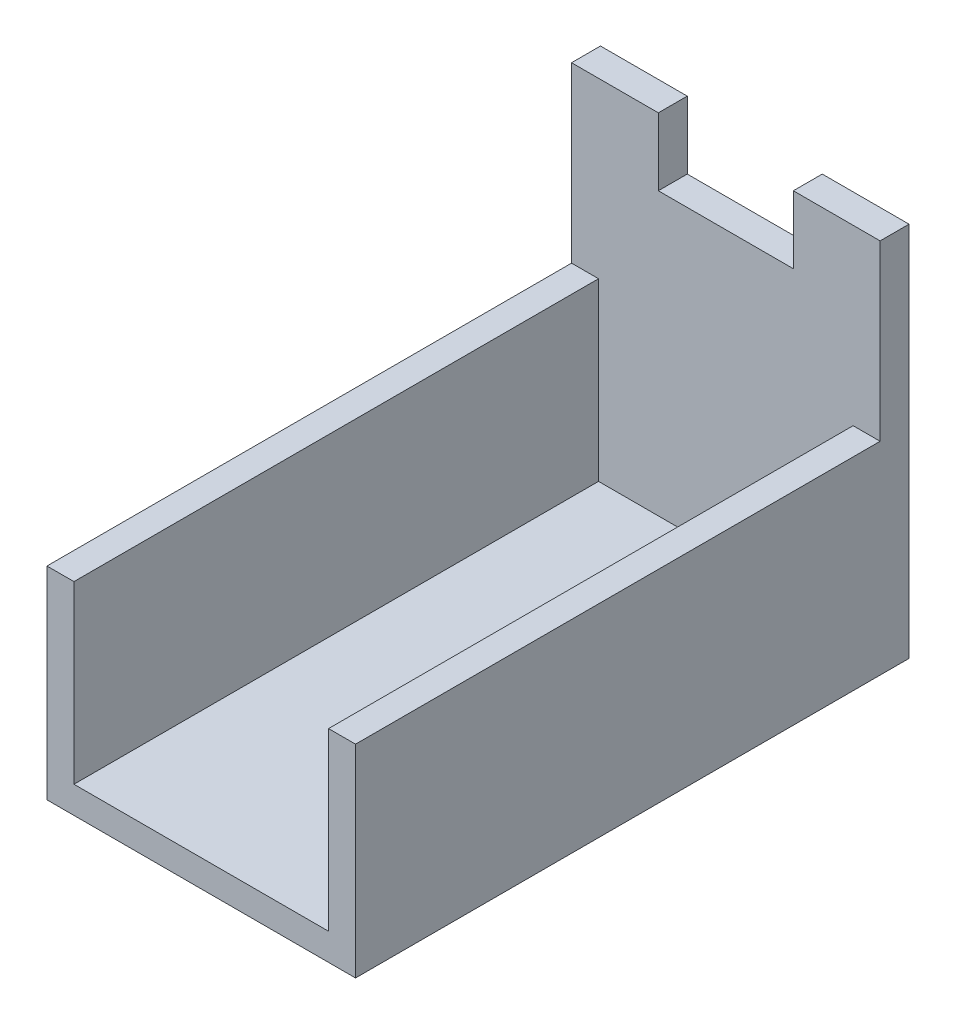
SolidWorks part; units mm, degrees
ref_plane "Front Plane" through (0, 0, 0) normal (0, 0, 1) x (1, 0, 0)
ref_plane "Top Plane" through (0, 0, 0) normal (0, 1, 0) x (1, 0, 0)
ref_plane "Right Plane" through (0, 0, 0) normal (1, 0, 0) x (0, 0, -1)
sketch "Sketch1" plane through (0, 0, 0) normal (0, 0, 1) x (1, 0, 0)
  line L0 (-1.524, 1.6923) -> (-1.524, 13.2493)
  line L1 (-1.524, 13.2493) -> (0.254, 13.2493)
  line L2 (0.254, 13.2493) -> (0.254, -0.0857)
  line L3 (0.254, -0.0857) -> (-20.066, -0.0857)
  line L4 (-20.066, -0.0857) -> (-20.066, 13.2493)
  line L5 (-20.066, 13.2493) -> (-18.288, 13.2493)
  line L6 (-18.288, 13.2493) -> (-18.288, 1.6923)
  line L7 (-18.288, 1.6923) -> (-1.524, 1.6923)
  point P2 (0, 0)
  dimension "D1" = 11.557
  dimension "D2" = 16.764
extrude "Boss-Extrude1" add sketch "Sketch1" against normal blind 36.449
sketch "Sketch3" plane through (0, 1.6923, 0) normal (0, 1, 0) x (1, 0, 0)
  line L0 (-18.288, 36.449) -> (-1.524, 36.449)
  line L1 (-1.524, 36.449) -> (-1.524, 34.544)
  line L2 (-1.524, 36.449) -> (-1.524, 0) construction
  line L3 (-1.524, 34.544) -> (-18.288, 34.544)
  line L4 (-18.288, 36.449) -> (-18.288, 0) construction
  line L5 (-18.288, 34.544) -> (-18.288, 36.449)
extrude "Boss-Extrude3" add sketch "Sketch3" along normal up to surface (11.557 mm away) up to face at (-19.177, 13.2493, -18.2245)
sketch "Sketch4" plane through (0, 13.2493, 0) normal (0, 1, 0) x (1, 0, 0)
  line L0 (-9.906, 34.544) -> (0.254, 34.544)
  line L1 (-18.288, 34.544) -> (-1.524, 34.544) construction
  line L2 (0.254, 36.449) -> (0.254, 0) construction
  line L3 (0.254, 34.544) -> (0.254, 36.449)
  line L4 (0.254, 36.449) -> (-20.066, 36.449)
  line L5 (-20.066, 36.449) -> (-20.066, 34.544)
  line L6 (-20.066, 36.449) -> (-20.066, 0) construction
  line L7 (-20.066, 34.544) -> (-9.906, 34.544)
extrude "Boss-Extrude4" add sketch "Sketch4" along normal blind 11.43
sketch "Sketch5" plane through (0, 0, -36.449) normal (0, 0, -1) x (-1, 0, 0)
  line L0 (9.906, 24.6793) -> (14.351, 24.6793)
  line L1 (-0.254, 24.6793) -> (20.066, 24.6793) construction
  line L2 (14.351, 24.6793) -> (14.351, 20.2343)
  line L3 (14.351, 20.2343) -> (5.461, 20.2343)
  line L4 (5.461, 20.2343) -> (5.461, 24.6793)
  line L5 (5.461, 24.6793) -> (9.906, 24.6793)
extrude "Cut-Extrude1" cut sketch "Sketch5" against normal up to next
